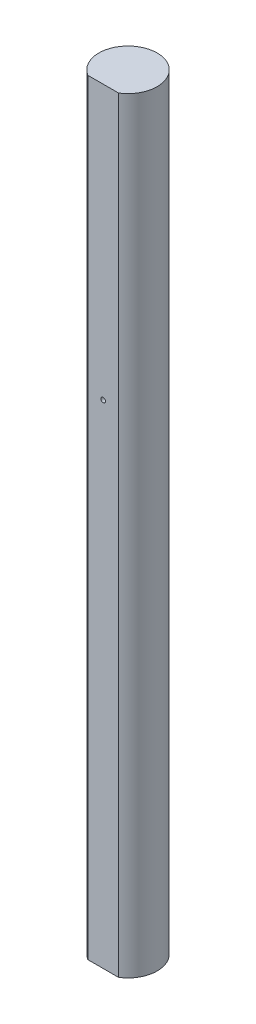
SolidWorks part; units mm, degrees
ref_plane "Front Plane" through (0, 0, 0) normal (0, 0, 1) x (1, 0, 0)
ref_plane "Top Plane" through (0, 0, 0) normal (0, 1, 0) x (1, 0, 0)
ref_plane "Right Plane" through (0, 0, 0) normal (1, 0, 0) x (0, 0, -1)
sketch "Sketch3" plane through (0, 0, 0) normal (0, 1, 0) x (1, 0, 0)
  line L0 (-10, -16.2143) -> (10, -16.2143)
  arc A0 (10, -16.2143) -> (-10, -16.2143) centre (0, 0) ccw
  dimension "D1" = 38.1
  dimension "D2" = 20
extrude "Boss-Extrude1" add sketch "Sketch3" along normal blind 500
sketch "Sketch5" plane through (0, 0, 16.2143) normal (0, 0, 1) x (1, 0, 0)
  line L0 (-10, 0) -> (10, 0) construction
  circle A0 centre (0, 321.4) radius 1.5
  dimension "D1" = 3
  dimension "D2" = 321.4
extrude "Cut-Extrude1" cut sketch "Sketch5" against normal blind 5
hole_wizard "M5x0.8 Tapped Hole1" positions "Sketch8" profile "Sketch9" tap size "M5x0.8" standard "ANSI Metric"
sketch "Sketch8" plane through (0, 0, 0) normal (0, -1, 0) x (-1, 0, 0)
  point P0 (0, 0)
sketch "Sketch9" plane through (0, 0, 0) normal (1, 0, 0) x (0, 0, -1)
  line L0 (0, 0) -> (0, 11.2618)
  line L1 (0, 11.2618) -> (2.1, 10)
  line L2 (2.1, 10) -> (2.1, 0)
  line L5 (2.1, 0) -> (0, 0)
  line L10 (0, 11.2618) -> (-2.1, 10) construction
  line L11 (0, -6.35) -> (0, 107.95) construction
  dimension "Tap Drill Dia." = 4.2
  dimension "Tap Drill Depth" = 10
  dimension "Drill Angle" = 118
cosmetic thread "Hole Thread1" parameters "D1"=10, "D2"=5
sketch "Sketch6" plane through (0, 0, 0) normal (0, -1, 0) x (1, 0, 0)
  line L1 (-38.1, -38.1) -> (38.1, -38.1)
  line L2 (-38.1, -38.1) -> (-38.1, 38.1)
  line L3 (-38.1, 38.1) -> (38.1, 38.1)
  line L4 (38.1, -38.1) -> (38.1, 38.1)
  line L5 (-38.1, -38.1) -> (38.1, 38.1) construction
  line L6 (-38.1, 38.1) -> (38.1, -38.1) construction
  point P0 (0, 0)
  dimension "D1" = 76.2
extrude "Boss-Extrude2" [suppressed] add sketch "Sketch6" along normal blind 9.144
sketch "Sketch7" [suppressed] plane through (0, -9.144, 0) normal (0, -1, 0) x (1, 0, 0)
  line L1 (-25, -25) -> (25, -25) construction
  line L2 (-25, -25) -> (-25, 25) construction
  line L3 (-25, 25) -> (25, 25) construction
  line L4 (25, -25) -> (25, 25) construction
  line L5 (-25, -25) -> (25, 25) construction
  line L6 (-25, 25) -> (25, -25) construction
  circle A0 centre (-25, 25) radius 1.65
  circle A1 centre (25, 25) radius 1.65
  circle A2 centre (25, -25) radius 1.65
  circle A3 centre (-25, -25) radius 1.65
  point P3 (0, 0)
  dimension "D1" = 3.3
  dimension "D2" = 50
extrude "Cut-Extrude2" [suppressed] cut sketch "Sketch7" against normal up to surface (9.144 mm away)
fillet "Fillet1" [suppressed] radius 5
equation "\"shaftDia\" = 38.1"
equation "\"D1@Sketch3\"=\"shaftDia\""
